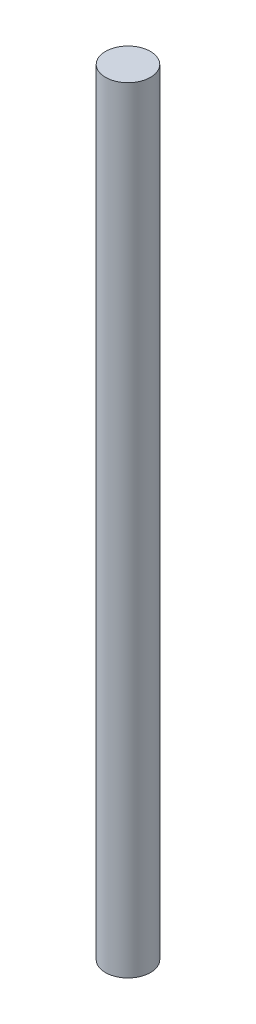
SolidWorks part; units mm, degrees
ref_plane "Front Plane" through (0, 0, 0) normal (0, 0, 1) x (1, 0, 0)
ref_plane "Top Plane" through (0, 0, 0) normal (0, 1, 0) x (1, 0, 0)
ref_plane "Right Plane" through (0, 0, 0) normal (1, 0, 0) x (0, 0, -1)
sketch "Sketch1" plane through (0, 0, 0) normal (0, 1, 0) x (1, 0, 0)
  circle A0 centre (0, 0) radius 1.45
  dimension "D1" = 2.9
extrude "Boss-Extrude1" add sketch "Sketch1" along normal blind 50
